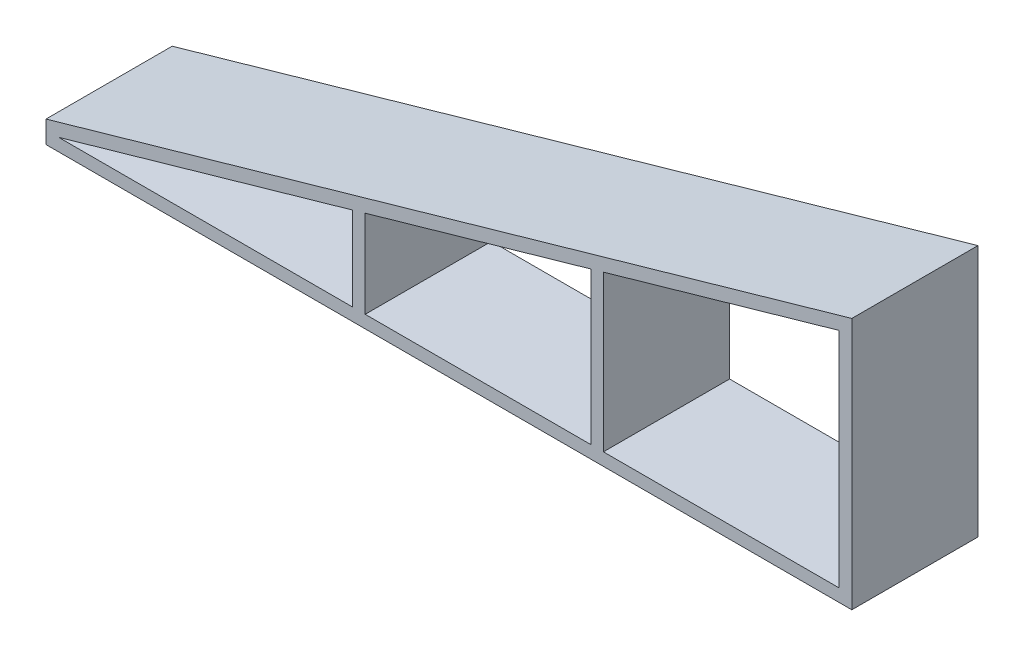
SolidWorks part; units mm, degrees
ref_plane "Front Plane" through (0, 0, 0) normal (0, 0, 1) x (1, 0, 0)
ref_plane "Top Plane" through (0, 0, 0) normal (0, 1, 0) x (1, 0, 0)
ref_plane "Right Plane" through (0, 0, 0) normal (1, 0, 0) x (0, 0, -1)
sketch "Sketch1" plane through (0, 0, 0) normal (0, 0, 1) x (1, 0, 0)
  line L0 (28.48, 5.5859) -> (28.48, -14.4141)
  line L1 (28.48, -14.4141) -> (-35.3799, -14.4141)
  line L2 (-35.3799, -12.6598) -> (28.48, 5.5859)
  line L3 (27.48, 4.2601) -> (27.48, -13.4141)
  line L4 (27.48, -13.4141) -> (8.7949, -13.4141)
  line L5 (8.7949, -13.4141) -> (8.7949, -1.0785)
  line L6 (8.7949, -1.0785) -> (27.48, 4.2601)
  line L7 (7.7949, -1.3642) -> (7.7949, -13.4141)
  line L8 (7.7949, -13.4141) -> (-10.0834, -13.4141)
  line L9 (-10.0834, -13.4141) -> (-10.0834, -6.4723)
  line L10 (-10.0834, -6.4723) -> (7.7949, -1.3642)
  line L11 (-11.0834, -6.758) -> (-11.0834, -13.4141)
  line L12 (-11.0834, -13.4141) -> (-34.3799, -13.4141)
  line L13 (-34.3799, -13.4141) -> (-11.0834, -6.758)
  line L14 (8.7949, -1.0785) -> (7.7949, -1.3642) construction
  line L15 (-10.0834, -6.4723) -> (-11.0834, -6.758) construction
  line L16 (-11.0834, -13.4141) -> (-10.0834, -13.4141) construction
  line L17 (7.7949, -13.4141) -> (8.7949, -13.4141) construction
  line L22 (-35.3799, -14.4141) -> (-35.3799, -12.6598)
  point P13 (-11.0834, -10.0861)
  dimension "D1" = 1
  dimension "D2" = 20
  dimension "D3" = 1
  dimension "D4" = 1
  dimension "D5" = 1
  dimension "D6" = 1
  dimension "D7" = 1
extrude "Boss-Extrude1" add sketch "Sketch1" along normal blind 10
